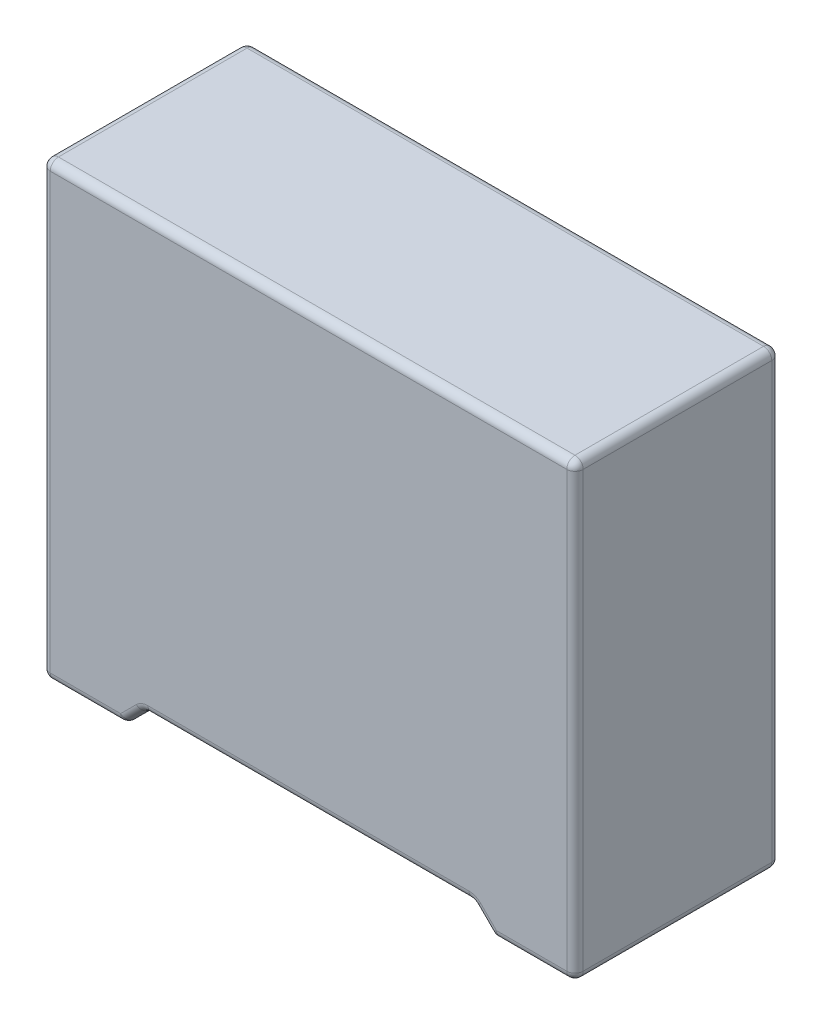
SolidWorks part; units mm, degrees
ref_plane "Front Plane" through (0, 0, 0) normal (0, 0, 1) x (1, 0, 0)
ref_plane "Top Plane" through (0, 0, 0) normal (0, 1, 0) x (1, 0, 0)
ref_plane "Right Plane" through (0, 0, 0) normal (1, 0, 0) x (0, 0, -1)
sketch "Sketch1" plane through (0, 0, 0) normal (0, 1, 0) x (1, 0, 0)
  line L0 (6.5, -2.5) -> (-6.5, 2.5) construction
  line L1 (-6.5, 2.5) -> (6.5, 2.5)
  line L2 (-6.5, 2.5) -> (-6.5, -2.5)
  line L3 (-6.5, -2.5) -> (6.5, -2.5)
  line L4 (6.5, 2.5) -> (6.5, -2.5)
  dimension "D1" = 13
  dimension "D2" = 5
extrude "Boss-Extrude1" add sketch "Sketch1" along normal blind 11
sketch "Sketch2" plane through (0, 0, 2.5) normal (0, 0, 1) x (1, 0, 0)
  line L0 (-4.5, 0) -> (-4, 0.5)
  line L1 (-6.5, 0) -> (6.5, 0) construction
  line L2 (-4, 0.5) -> (4, 0.5)
  line L3 (4, 0.5) -> (4.5, 0)
  line L4 (4.5, 0) -> (4.5, -1.5)
  line L5 (4.5, -1.5) -> (-4.5, -1.5)
  line L6 (-4.5, -1.5) -> (-4.5, 0)
  line L7 (0, 0) -> (0, 0.5) construction
  dimension "D1" = 2
  dimension "D2" = 0.5
  dimension "D3" = 45
  dimension "D4" = 2
extrude "Cut-Extrude1" cut sketch "Sketch2" against normal through all
sketch "Sketch3" plane through (0, 0, 0) normal (0, -1, 0) x (1, 0, 0)
  line L0 (-5, 0) -> (5, 0) construction
  circle A0 centre (5, 0) radius 0.3
  circle A1 centre (-5, 0) radius 0.3
  dimension "D1" = 0.6
  dimension "D2" = 10
extrude "Boss-Extrude2" add sketch "Sketch3" along normal blind 1
fillet "Fillet1" radius 0.2 24 edges at (6.5, 0, 0) (4.25, 0.25, -2.5) (5.5, 0, -2.5) (6.5, 5.5, -2.5) (-5.5, 0, -2.5) (-4.25, 0.25, -2.5) (0, 0.5, -2.5) (-6.5, 5.5, -2.5) (-6.5, 0, 0) (0, 11, -2.5) (6.5, 11, 0) (-6.5, 11, 0) (-6.5, 5.5, 2.5) (0, 11, 2.5) (6.5, 5.5, 2.5) (5.5, 0, 2.5) (4.25, 0.25, 2.5) (0, 0.5, 2.5) (-4.25, 0.25, 2.5) (-5.5, 0, 2.5) (4.5, 0, 0) (-4.5, 0, 0) (-4, 0.5, 0) (4, 0.5, 0)
